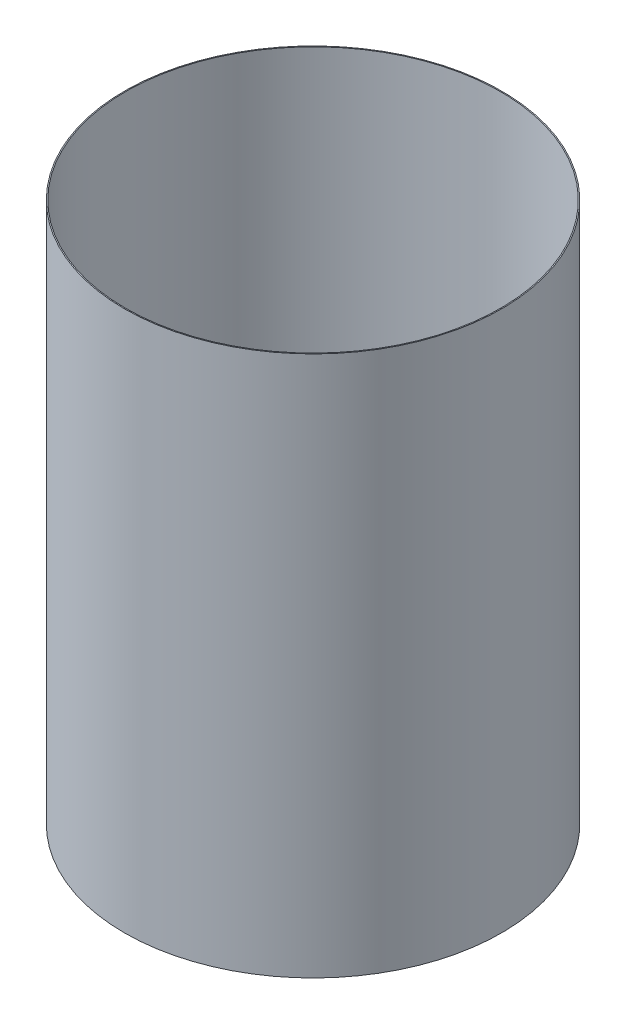
SolidWorks part; units mm, degrees
material "Thornel Mat VMA"
ref_plane "Front Plane" through (0, 0, 0) normal (0, 0, 1) x (1, 0, 0)
ref_plane "Top Plane" through (0, 0, 0) normal (0, 1, 0) x (1, 0, 0)
ref_plane "Right Plane" through (0, 0, 0) normal (1, 0, 0) x (0, 0, -1)
ref_axis "Axis1" through (0, 55, 0) along (0, -1, 0)
sketch "Sketch1" plane through (0, 0, 0) normal (0, 0, 1) x (1, 0, 0)
  line L0 (-46.2851, -19.9059) -> (-46.2851, -153.2559)
  line L2 (-38.1, -19.9059) -> (0, -19.9059) construction
  line L3 (-38.1, -153.2559) -> (0, -153.2559) construction
revolve "Revolve-Thin1" add sketch "Sketch1" angle 360 about axis through (0, 55, 0) along (0, -1, 0)
equation "\"D3@Revolve-Thin1\"=\"CF THICKNESS@Cryo Tank.Assembly\""
